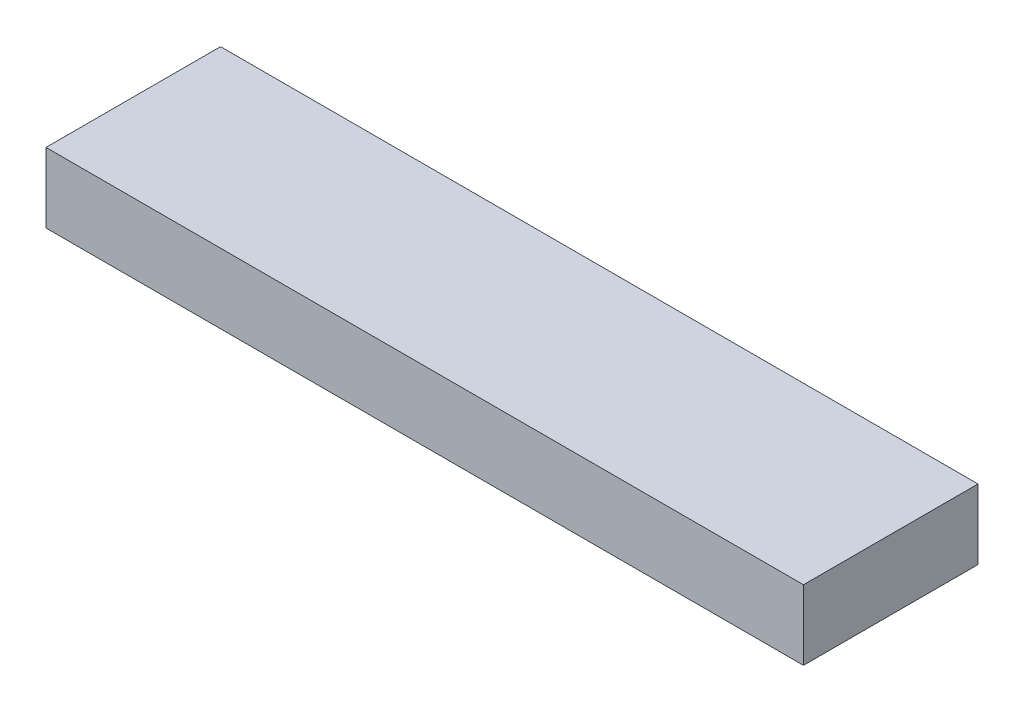
SolidWorks part; units mm, degrees
ref_plane "Front Plane" through (0, 0, 0) normal (0, 0, 1) x (1, 0, 0)
ref_plane "Top Plane" through (0, 0, 0) normal (0, 1, 0) x (1, 0, 0)
ref_plane "Right Plane" through (0, 0, 0) normal (1, 0, 0) x (0, 0, -1)
sketch "Sketch1" plane through (0, 0, 0) normal (0, 1, 0) x (1, 0, 0)
  line L1 (0, 0) -> (2.17, 0)
  line L2 (0, 0) -> (0, 0.5)
  line L3 (0, 0.5) -> (2.17, 0.5)
  line L4 (2.17, 0) -> (2.17, 0.5)
extrude "Boss-Extrude1" add sketch "Sketch1" along normal blind 0.2
